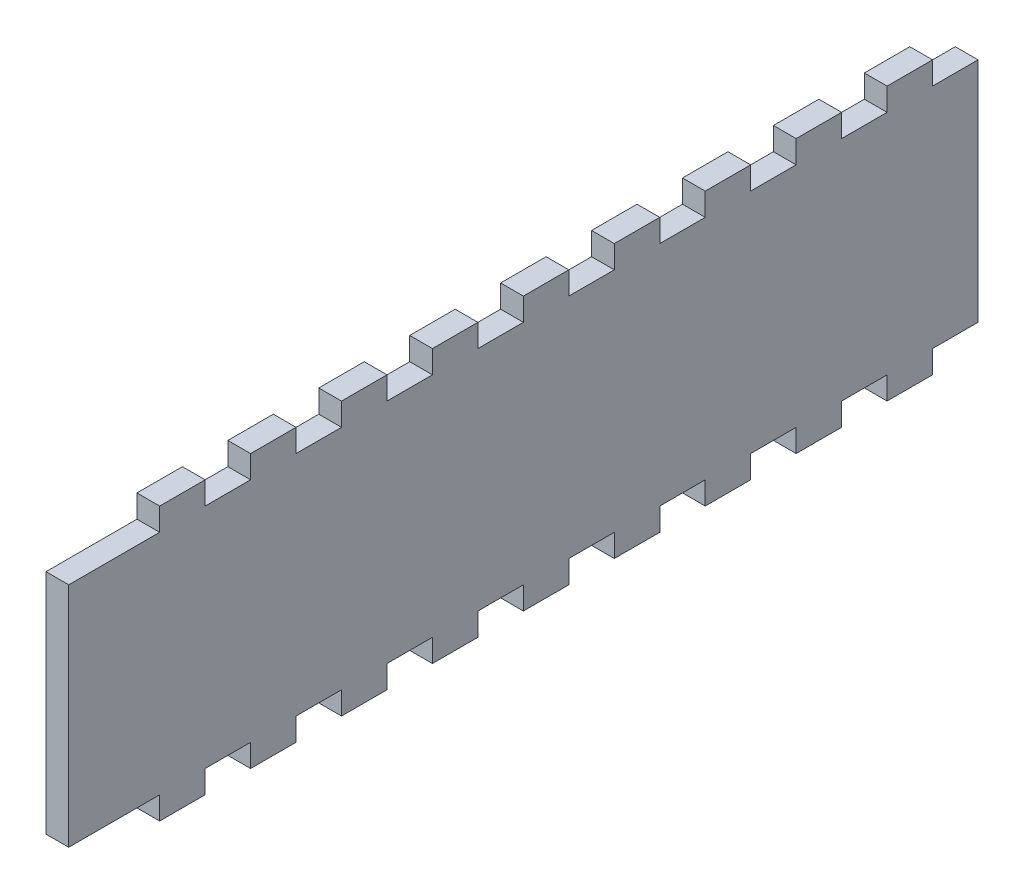
SolidWorks part; units mm, degrees
ref_plane "Front Plane" through (0, 0, 0) normal (0, 0, 1) x (1, 0, 0)
ref_plane "Top Plane" through (0, 0, 0) normal (0, 1, 0) x (1, 0, 0)
ref_plane "Right Plane" through (0, 0, 0) normal (1, 0, 0) x (0, 0, -1)
sketch "Sketch1" plane through (0, 0, 0) normal (1, 0, 0) x (0, 0, -1)
  line L0 (40, 50) -> (40, 55)
  line L1 (0, 0) -> (20, 0)
  line L2 (0, 0) -> (0, 50)
  line L3 (0, 50) -> (20, 50)
  line L4 (200, 0) -> (200, 50)
  line L5 (50, 50) -> (60, 50)
  line L6 (20, 50) -> (20, 55)
  line L7 (20, 55) -> (30, 55)
  line L8 (30, 50) -> (30, 55)
  line L9 (50, 50) -> (50, 55)
  line L10 (40, 55) -> (50, 55)
  line L11 (60, 50) -> (60, 55)
  line L12 (70, 50) -> (70, 55)
  line L13 (60, 55) -> (70, 55)
  line L14 (80, 50) -> (80, 55)
  line L15 (90, 50) -> (90, 55)
  line L16 (80, 55) -> (90, 55)
  line L17 (100, 50) -> (100, 55)
  line L18 (110, 50) -> (110, 55)
  line L19 (100, 55) -> (110, 55)
  line L20 (120, 50) -> (120, 55)
  line L21 (130, 50) -> (130, 55)
  line L22 (120, 55) -> (130, 55)
  line L23 (140, 50) -> (140, 55)
  line L24 (150, 50) -> (150, 55)
  line L25 (140, 55) -> (150, 55)
  line L26 (160, 50) -> (160, 55)
  line L27 (170, 50) -> (170, 55)
  line L28 (160, 55) -> (170, 55)
  line L29 (180, 50) -> (180, 55)
  line L30 (190, 50) -> (190, 55)
  line L31 (180, 55) -> (190, 55)
  line L32 (40, -5) -> (40, 0)
  line L33 (50, -5) -> (50, 0)
  line L34 (30, 0) -> (40, 0)
  line L35 (60, -5) -> (60, 0)
  line L36 (70, -5) -> (70, 0)
  line L37 (50, 0) -> (60, 0)
  line L38 (80, -5) -> (80, 0)
  line L39 (90, -5) -> (90, 0)
  line L40 (70, 0) -> (80, 0)
  line L41 (100, -5) -> (100, 0)
  line L42 (110, -5) -> (110, 0)
  line L43 (90, 0) -> (100, 0)
  line L44 (120, -5) -> (120, 0)
  line L45 (130, -5) -> (130, 0)
  line L46 (110, 0) -> (120, 0)
  line L47 (140, -5) -> (140, 0)
  line L48 (150, -5) -> (150, 0)
  line L49 (130, 0) -> (140, 0)
  line L50 (160, -5) -> (160, 0)
  line L51 (170, -5) -> (170, 0)
  line L52 (20, -5) -> (30, -5)
  line L53 (180, -5) -> (180, 0)
  line L54 (190, -5) -> (190, 0)
  line L55 (40, -5) -> (50, -5)
  line L56 (20, -5) -> (20, 0)
  line L57 (30, -5) -> (30, 0)
  line L58 (60, -5) -> (70, -5)
  line L59 (30, 50) -> (40, 50)
  line L60 (70, 50) -> (80, 50)
  line L61 (90, 50) -> (100, 50)
  line L62 (110, 50) -> (120, 50)
  line L63 (130, 50) -> (140, 50)
  line L64 (150, 50) -> (160, 50)
  line L65 (170, 50) -> (180, 50)
  line L66 (190, 50) -> (200, 50)
  line L67 (190, 0) -> (200, 0)
  line L68 (170, 0) -> (180, 0)
  line L69 (150, 0) -> (160, 0)
  line L70 (140, 0) -> (150, 0) [skipped]
  line L71 (160, 0) -> (170, 0) [skipped]
  line L72 (180, 0) -> (190, 0) [skipped]
  line L73 (120, 0) -> (130, 0) [skipped]
  line L74 (100, 0) -> (110, 0) [skipped]
  line L75 (80, 0) -> (90, 0) [skipped]
  line L76 (60, 0) -> (70, 0) [skipped]
  line L77 (40, 0) -> (50, 0) [skipped]
  line L78 (20, 0) -> (30, 0) [skipped]
  line L79 (80, -5) -> (90, -5)
  line L80 (100, -5) -> (110, -5)
  line L81 (120, -5) -> (130, -5)
  line L82 (140, -5) -> (150, -5)
  line L83 (160, -5) -> (170, -5)
  line L84 (180, -5) -> (190, -5)
  dimension "D1" = 50
  dimension "D2" = 200
  dimension "D3" = 20
  dimension "D4" = 5
  dimension "D5" = 10
  dimension "D6" = 2
extrude "Boss-Extrude1" add sketch "Sketch1" along normal blind 5
